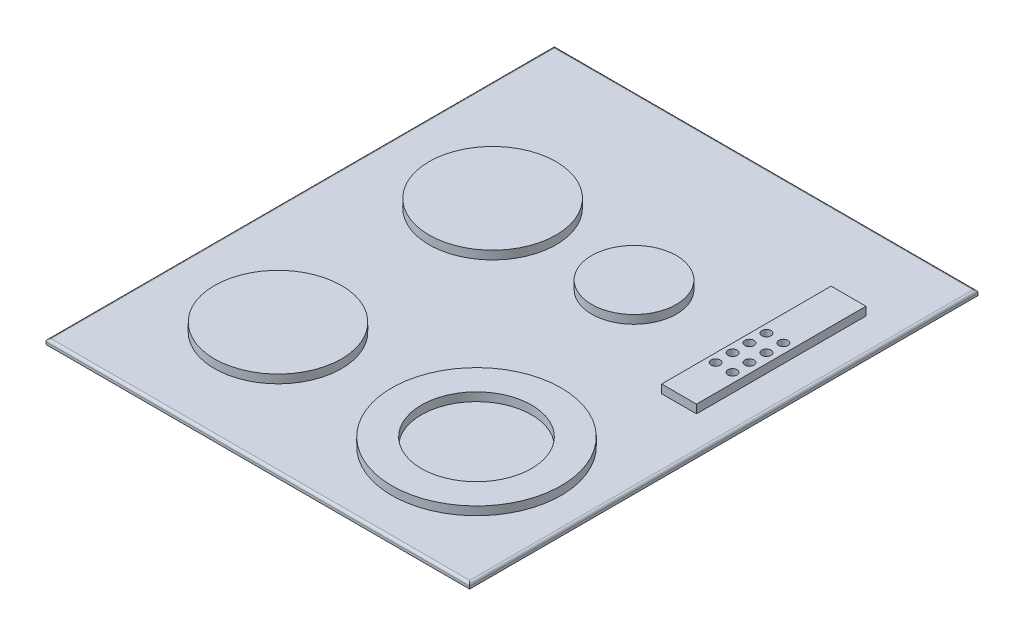
SolidWorks part; units mm, degrees
ref_plane "Front Plane" through (0, 0, 0) normal (0, 0, 1) x (1, 0, 0)
ref_plane "Top Plane" through (0, 0, 0) normal (0, 1, 0) x (1, 0, 0)
ref_plane "Right Plane" through (0, 0, 0) normal (1, 0, 0) x (0, 0, -1)
sketch "Sketch1" plane through (0, 0, 0) normal (0, 1, 0) x (1, 0, 0)
  line L1 (0, 0) -> (500, 0)
  line L2 (0, 0) -> (0, 600)
  line L3 (0, 600) -> (500, 600)
  line L4 (500, 0) -> (500, 600)
  dimension "D1" = 500
  dimension "D2" = 600
extrude "Boss-Extrude1" add sketch "Sketch1" along normal blind 6
fillet "Fillet1" radius 3 4 edges at (250, 6, -600) (500, 6, -300) (250, 6, 0) (0, 6, -300)
sketch "Sketch2" plane through (0, 6, 0) normal (0, 1, 0) x (1, 0, 0)
  line L0 (497, 597) -> (3, 597) construction
  line L1 (419.6467, 507) -> (460.7512, 507)
  line L2 (419.6467, 507) -> (419.6467, 307)
  line L3 (419.6467, 307) -> (460.7512, 307)
  line L4 (460.7512, 507) -> (460.7512, 307)
  line L5 (3, 597) -> (3, 3) construction
  line L6 (3, 3) -> (497, 3) construction
  line L7 (497, 3) -> (497, 597) construction
  circle A0 centre (130.0893, 397) radius 75
  circle A1 centre (297, 397) radius 50
  circle A2 centre (130.0893, 143.7401) radius 75
  circle A3 centre (364.3301, 143.7401) radius 100
  circle A4 centre (364.3301, 143.7401) radius 65
  circle A5 centre (449.544, 420.752) radius 5.3994
  circle A6 centre (429.544, 420.752) radius 5.3994
  circle A7 centre (429.544, 400.752) radius 5.3994
  circle A8 centre (429.544, 380.752) radius 5.3994
  circle A9 centre (429.544, 360.752) radius 5.3994
  circle A10 centre (449.544, 400.752) radius 5.3994
  circle A11 centre (449.544, 380.752) radius 5.3994
  circle A12 centre (449.544, 360.752) radius 5.3994
  point P39 (440.199, 507)
  dimension "D1" = 150
  dimension "D2" = 150
  dimension "D3" = 200
  dimension "D4" = 130
  dimension "D5" = 100
  dimension "D6" = 2
  dimension "D8" = 200
  dimension "D9" = 127.0893
  dimension "D10" = 140.7401
  dimension "D11" = 127.0893
  dimension "D12" = 140.7401
  dimension "D13" = 132.6699
  dimension "D14" = 200
  dimension "D15" = 200
  dimension "D16" = 200
  dimension "D17" = 90
  dimension "D18" = 11.2073
  dimension "D19" = 86.248
  dimension "D20" = 67.456
  dimension "D21" = 86.248
  dimension "D22" = 11.2073
  dimension "D23" = 9.8972
  dimension "D24" = 106.248
  dimension "D7" = 4
sketch "Sketch3" plane through (0, 0, 0) normal (0, -1, 0) x (1, 0, 0)
  line L0 (450, -50) -> (50, -50)
  line L1 (50, -50) -> (50, -550)
  line L2 (50, -550) -> (450, -550)
  line L3 (450, -550) -> (450, -50)
  line L4 (0, 0) -> (0, -600)
  line L5 (0, -600) -> (500, -600)
  line L6 (500, -600) -> (500, 0)
  line L7 (500, 0) -> (0, 0)
  line L8 (0, 0) -> (0, -600)
  line L9 (0, -600) -> (500, -600)
  line L10 (500, -600) -> (500, 0)
  line L11 (500, 0) -> (0, 0)
  dimension "D1" = 0
  dimension "D2" = 50
extrude "Boss-Extrude2" add sketch "Sketch3" along normal blind 26 contours L2 L3 L0 L1
extrude "Boss-Extrude3" add sketch "Sketch2" along normal blind 10
sketch "Sketch4" plane through (0, -26, 0) normal (0, -1, 0) x (1, 0, 0)
  line L0 (450, -50) -> (50, -50) construction
  line L1 (50, -50) -> (50, -550) construction
  circle A0 centre (250, -300) radius 53.9662
  dimension "D1" = 250
  dimension "D2" = 200
extrude "Boss-Extrude4" add sketch "Sketch4" along normal blind 1
